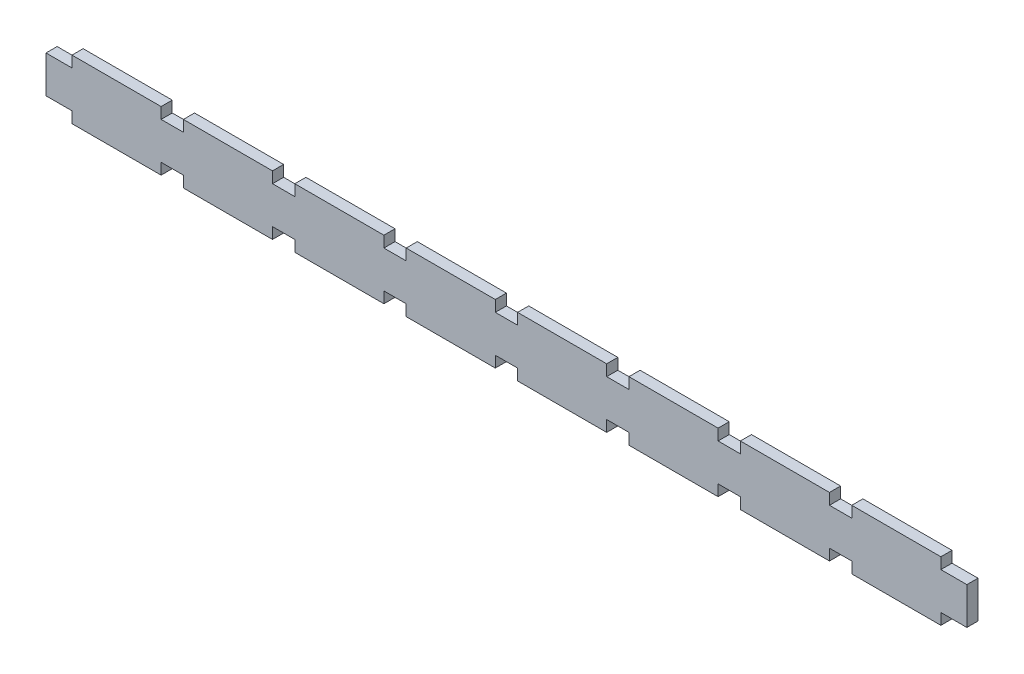
SolidWorks part; units mm, degrees
ref_plane "Front Plane" through (0, 0, 0) normal (0, 0, 1) x (1, 0, 0)
ref_plane "Top Plane" through (0, 0, 0) normal (0, 1, 0) x (1, 0, 0)
ref_plane "Right Plane" through (0, 0, 0) normal (1, 0, 0) x (0, 0, -1)
sketch "Sketch1" plane through (0, 0, 0) normal (0, 0, 1) x (-1, 0, 0)
  line L1 (545.7872, 3) -> (545.7872, 0)
  line L8 (311.7872, 0) -> (335.7872, 0)
  line L10 (552.7872, 3) -> (545.7872, 3)
  line L25 (311.7872, 3) -> (311.7872, 0)
  line L26 (335.7872, 3) -> (335.7872, 0)
  line L27 (341.7872, 3) -> (341.7872, 0)
  line L28 (365.7872, 3) -> (365.7872, 0)
  line L29 (371.7872, 3) -> (371.7872, 0)
  line L30 (395.7872, 3) -> (395.7872, 0)
  line L31 (401.7872, 3) -> (401.7872, 0)
  line L32 (425.7872, 3) -> (425.7872, 0)
  line L33 (431.7872, 3) -> (431.7872, 0)
  line L34 (455.7872, 3) -> (455.7872, 0)
  line L35 (461.7872, 3) -> (461.7872, 0)
  line L36 (485.7872, 3) -> (485.7872, 0)
  line L37 (491.7872, 3) -> (491.7872, 0)
  line L38 (515.7872, 3) -> (515.7872, 0)
  line L39 (521.7872, 3) -> (521.7872, 0)
  line L40 (521.7872, 0) -> (545.7872, 0)
  line L41 (491.7872, 0) -> (515.7872, 0)
  line L42 (461.7872, 0) -> (485.7872, 0)
  line L43 (431.7872, 0) -> (455.7872, 0)
  line L44 (401.7872, 0) -> (425.7872, 0)
  line L45 (371.7872, 0) -> (395.7872, 0)
  line L46 (341.7872, 0) -> (365.7872, 0)
  line L47 (304.7872, 3) -> (304.7872, 13)
  line L48 (299.261, 8) -> (304.7872, 8) construction
  line L49 (545.7872, 13) -> (545.7872, 16)
  line L50 (521.7872, 16) -> (545.7872, 16)
  line L51 (521.7872, 13) -> (521.7872, 16)
  line L52 (515.7872, 13) -> (515.7872, 16)
  line L53 (491.7872, 16) -> (515.7872, 16)
  line L54 (491.7872, 13) -> (491.7872, 16)
  line L55 (485.7872, 13) -> (485.7872, 16)
  line L56 (461.7872, 16) -> (485.7872, 16)
  line L57 (461.7872, 13) -> (461.7872, 16)
  line L58 (455.7872, 13) -> (455.7872, 16)
  line L59 (431.7872, 16) -> (455.7872, 16)
  line L60 (431.7872, 13) -> (431.7872, 16)
  line L61 (425.7872, 13) -> (425.7872, 16)
  line L62 (401.7872, 16) -> (425.7872, 16)
  line L63 (401.7872, 13) -> (401.7872, 16)
  line L64 (395.7872, 13) -> (395.7872, 16)
  line L65 (371.7872, 16) -> (395.7872, 16)
  line L66 (371.7872, 13) -> (371.7872, 16)
  line L67 (365.7872, 13) -> (365.7872, 16)
  line L68 (341.7872, 16) -> (365.7872, 16)
  line L69 (341.7872, 13) -> (341.7872, 16)
  line L70 (335.7872, 13) -> (335.7872, 16)
  line L71 (311.7872, 16) -> (335.7872, 16)
  line L72 (311.7872, 13) -> (311.7872, 16)
  line L73 (552.7872, 13) -> (545.7872, 13)
  line L74 (552.7872, 13) -> (552.7872, 3)
  line L75 (521.7872, 13) -> (515.7872, 13)
  line L76 (521.7872, 3) -> (515.7872, 3)
  line L77 (491.7872, 13) -> (485.7872, 13)
  line L78 (461.7872, 13) -> (455.7872, 13)
  line L79 (491.7872, 3) -> (485.7872, 3)
  line L80 (461.7872, 3) -> (455.7872, 3)
  line L81 (431.7872, 13) -> (425.7872, 13)
  line L82 (431.7872, 3) -> (425.7872, 3)
  line L83 (401.7872, 13) -> (395.7872, 13)
  line L84 (401.7872, 3) -> (395.7872, 3)
  line L85 (371.7872, 13) -> (365.7872, 13)
  line L86 (371.7872, 3) -> (365.7872, 3)
  line L87 (341.7872, 13) -> (335.7872, 13)
  line L88 (341.7872, 3) -> (335.7872, 3)
  line L89 (311.7872, 13) -> (304.7872, 13)
  line L90 (311.7872, 3) -> (304.7872, 3)
extrude "Boss-Extrude1" add sketch "Sketch1" along normal blind 3
